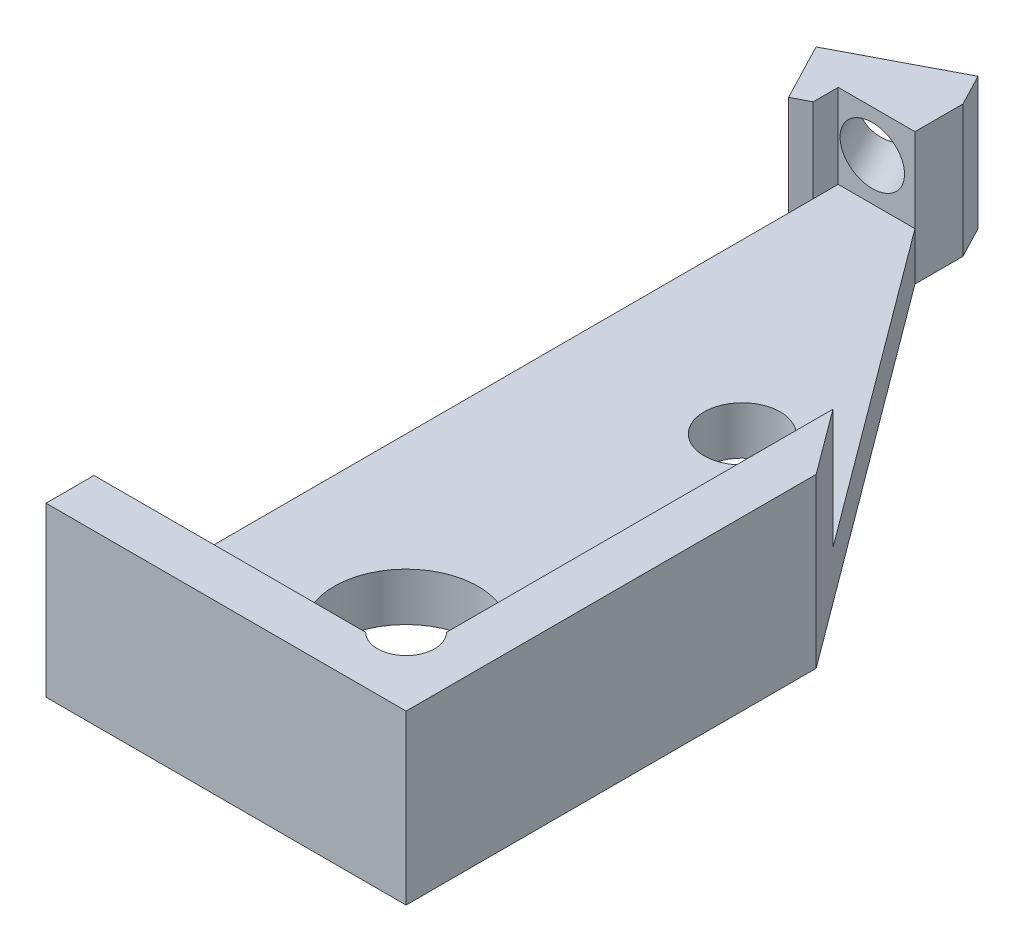
SolidWorks part; units mm, degrees
ref_plane "Front Plane" through (0, 0, 0) normal (0, 0, 1) x (1, 0, 0)
ref_plane "Top Plane" through (0, 0, 0) normal (0, 1, 0) x (1, 0, 0)
ref_plane "Right Plane" through (0, 0, 0) normal (1, 0, 0) x (0, 0, -1)
sketch "Sketch1" plane through (0, 0, 0) normal (0, 1, 0) x (1, 0, 0)
  line L7 (3.75, 8.75) -> (-3.75, 8.75)
  line L8 (3.75, 8.75) -> (3.75, -8.75)
  line L9 (3.75, -8.75) -> (-3.75, -8.75)
  line L10 (-3.75, 8.75) -> (-3.75, -8.75)
  line L11 (3.75, 8.75) -> (-3.75, -8.75) construction
  line L12 (3.75, -8.75) -> (-3.75, 8.75) construction
  point P0 (0, 0)
  point P6 (0, 0)
  dimension "D1" = 7.5
  dimension "D2" = 17.5
extrude "Boss-Extrude1" add sketch "Sketch1" along normal blind 3.5
sketch "Sketch2" plane through (0, 3.5, 0) normal (0, 1, 0) x (1, 0, 0)
  line L0 (-3.75, 8.75) -> (-3.75, -8.75) construction
  line L1 (2.75, 7.75) -> (-2.75, 7.75)
  line L2 (2.75, 7.75) -> (2.75, -7.75)
  line L3 (2.75, -7.75) -> (-2.75, -7.75)
  line L4 (-2.75, 7.75) -> (-2.75, -7.75)
  line L5 (2.75, 7.75) -> (-2.75, -7.75) construction
  line L6 (2.75, -7.75) -> (-2.75, 7.75) construction
  line L7 (3.75, 8.75) -> (-3.75, 8.75) construction
  point P0 (0, 0)
  dimension "D1" = 1
  dimension "D2" = 1
extrude "Cut-Extrude1" cut sketch "Sketch2" against normal offset from surface (2.5 mm away) 1 up to face at (0, 0, 0)
sketch "Sketch3" plane through (0, 1, 0) normal (0, 1, 0) x (1, 0, 0)
  line L0 (-2.75, -7.75) -> (2.75, -7.75) construction
  line L1 (2.75, -7.75) -> (2.75, 7.75) construction
  circle A0 centre (-0.25, -4.75) radius 1.5
  dimension "D1" = 3
  dimension "D2" = 3
  dimension "D3" = 3
extrude "GRIN Hole" cut sketch "Sketch3" against normal through all
sketch "Sketch6" plane through (0, 3.5, 0) normal (0, 1, 0) x (1, 0, 0)
  line L0 (2.75, -7.75) -> (2.75, 7.75) construction
  line L2 (-2.75, -7.75) -> (2.75, -7.75) construction
  line L3 (2.75, -7.3291) -> (2.3291, -7.3291) construction
  line L4 (2.3291, -7.3291) -> (2.3291, -7.75) construction
  circle A3 centre (2.3291, -7.3291) radius 0.5953
  dimension "D1" = 1.1906
extrude "Corner divot" cut sketch "Sketch6" against normal up to surface (2.5 mm away) up to face at (-0.25, 1, 6.25)
sketch "Sketch7" plane through (0, 1, 0) normal (0, 1, 0) x (1, 0, 0)
  line L0 (1.625, 2.25) -> (-2.125, 2.25) construction
  line L1 (-2.125, 2.25) -> (-2.125, -6.5) construction
  line L2 (-2.125, -6.5) -> (1.625, -6.5) construction
  line L3 (1.625, -6.5) -> (1.625, 2.25) construction
  line L4 (-0.25, 2.25) -> (-0.25, -4.75) construction
  circle A0 centre (-0.25, 2.25) radius 0.7938
  circle A2 centre (-2.125, -6.5) radius 0.7938
  circle A3 centre (1.625, -6.5) radius 0.7938
  circle A4 centre (-0.25, -4.75) radius 1.5 construction
  dimension "D1" = 1.5875
  dimension "D2" = 3.75
  dimension "D3" = 7
  dimension "D4" = 1.75
extrude "Magnet Holes" cut sketch "Sketch7" against normal through all
sketch "Sketch9" plane through (0, 3.5, 0) normal (0, 1, 0) x (1, 0, 0)
  line L0 (-2.494, 9.4054) -> (-4.7104, 8.2489)
  line L1 (-3.4577, 7.3807) -> (-4.0863, 7.0527)
  line L2 (-3.4577, 7.3807) -> (-2.4984, 7.8813)
  line L3 (-2.494, 9.4054) -> (-1.8698, 8.2093)
  line L4 (2.75, -4.0155) -> (-1.9462, 4.9845) construction
  line L5 (2.75, -4.0155) -> (-1.9462, -7.75) construction
  line L6 (-2.75, -7.75) -> (1.9081, -7.75) construction
  line L8 (-1.9462, -7.75) -> (-1.9462, 4.9845) construction
  line L9 (-1.9462, 4.9845) -> (2.75, 4.9845) construction
  line L10 (2.75, -6.9081) -> (2.75, 7.75) construction
  line L11 (2.75, 4.9845) -> (2.75, -4.0155) construction
  line L12 (-1.9462, 4.4839) -> (-0.9869, 4.9845) construction
  line L13 (-1.9462, 4.4839) -> (-3.4577, 7.3807) construction
  line L14 (-1.4665, 4.7342) -> (-2.9781, 7.631) construction
  line L15 (-1.8698, 8.2093) -> (-2.4984, 7.8813)
  line L16 (-4.0863, 7.0527) -> (-4.7104, 8.2489)
  line L17 (-2.9781, 7.631) -> (-3.6022, 8.8271) construction
  dimension "D1" = 6
  dimension "D2" = 9
  dimension "D3" = 1.082
  dimension "D4" = 2.5
extrude "Boss-Extrude2" add sketch "Sketch9" against normal up to surface (3.5 mm away) up to face at (1.625, 0, 7.2938)
sketch "Sketch14" plane through (0, 3.5, 0) normal (0, 1, 0) x (1, 0, 0)
  line L1 (-5.7326, 5.1835) -> (0.2326, 5.1835)
  line L2 (-5.7326, 5.1835) -> (-5.7326, 10.3165)
  line L3 (-5.7326, 10.3165) -> (0.2326, 10.3165)
  line L4 (0.2326, 5.1835) -> (0.2326, 10.3165)
  line L5 (-5.7326, 5.1835) -> (0.2326, 10.3165) construction
  line L6 (-5.7326, 10.3165) -> (0.2326, 5.1835) construction
  point P0 (-2.75, 7.75)
extrude "Set Screw Extension" cut sketch "Sketch14" against normal blind 0.75
sketch "Sketch10" plane through (-4.3911, 0, -8.4155) normal (-0.4626, 0, -0.8866) x (-0.8866, 0, 0.4626)
  line L0 (-0.8899, 1) -> (-0.8899, 1.875) construction
  line L1 (-2.1399, 2.75) -> (0.3601, 2.75) construction
  line L2 (-0.8899, 1.875) -> (-0.8899, 2.75) construction
  line L4 (-0.8899, 1) -> (-0.8899, 0) construction
  line L5 (-2.1399, 0) -> (0.3601, 0) construction
  dimension "D1" = 1
hole_wizard "Tap Drill for #0-80 Tap1" positions "Sketch12" profile "Sketch11" hole size "#0-80" standard "ANSI Inch"
sketch "Sketch12" plane through (-4.3911, 0, -8.4155) normal (-0.4626, 0, -0.8866) x (-0.8866, 0, 0.4626)
  point P0 (-0.8899, 1.875)
sketch "Sketch11" plane through (-3.6022, 1.875, -8.8271) normal (0, 1, 0) x (-0.8866, 0, 0.4626)
  line L0 (0, 0) -> (0, 7.4679)
  line L1 (0, 7.4679) -> (0.5956, 7.11)
  line L2 (0.5956, 7.11) -> (0.5956, 0)
  line L5 (0.5956, 0) -> (0, 0)
  line L10 (0, 7.4679) -> (-0.5956, 7.11) construction
  line L11 (0, -6.35) -> (0, 107.95) construction
  dimension "Hole Dia." = 1.1913
  dimension "Hole Depth" = 7.11
  dimension "Drill Angle" = 118
sketch "Sketch15" plane through (0, 0, 0) normal (0, 1, 0) x (1, 0, 0)
  line L2 (-2.152, 9.3132) -> (-2.152, 7.75)
  line L4 (2.75, 7.75) -> (-2.75, 7.75) construction
  line L5 (-2.152, 9.3132) -> (3.75, 9.3132)
  line L6 (3.75, 9.3132) -> (3.75, -0.2086)
  line L7 (-2.152, 7.75) -> (3.75, -0.2086)
  line L8 (3.75, -8.75) -> (3.75, 8.75) construction
extrude "Diagonal Cut" cut sketch "Sketch15" along normal blind 5
sketch "Sketch16" plane through (0, 1, 0) normal (0, 1, 0) x (1, 0, 0)
  line L0 (-3.75, -7.75) -> (-3.75, 7.75)
  line L1 (-3.75, 7.75) -> (-2.75, 7.75)
  line L2 (-2.75, 7.75) -> (-2.75, -7.75)
  line L3 (-2.75, -7.75) -> (-3.75, -7.75)
  line L6 (-3.75, 7.2282) -> (-3.75, -8.75) construction
extrude "Vertical Cut" cut sketch "Sketch16" along normal blind 3
